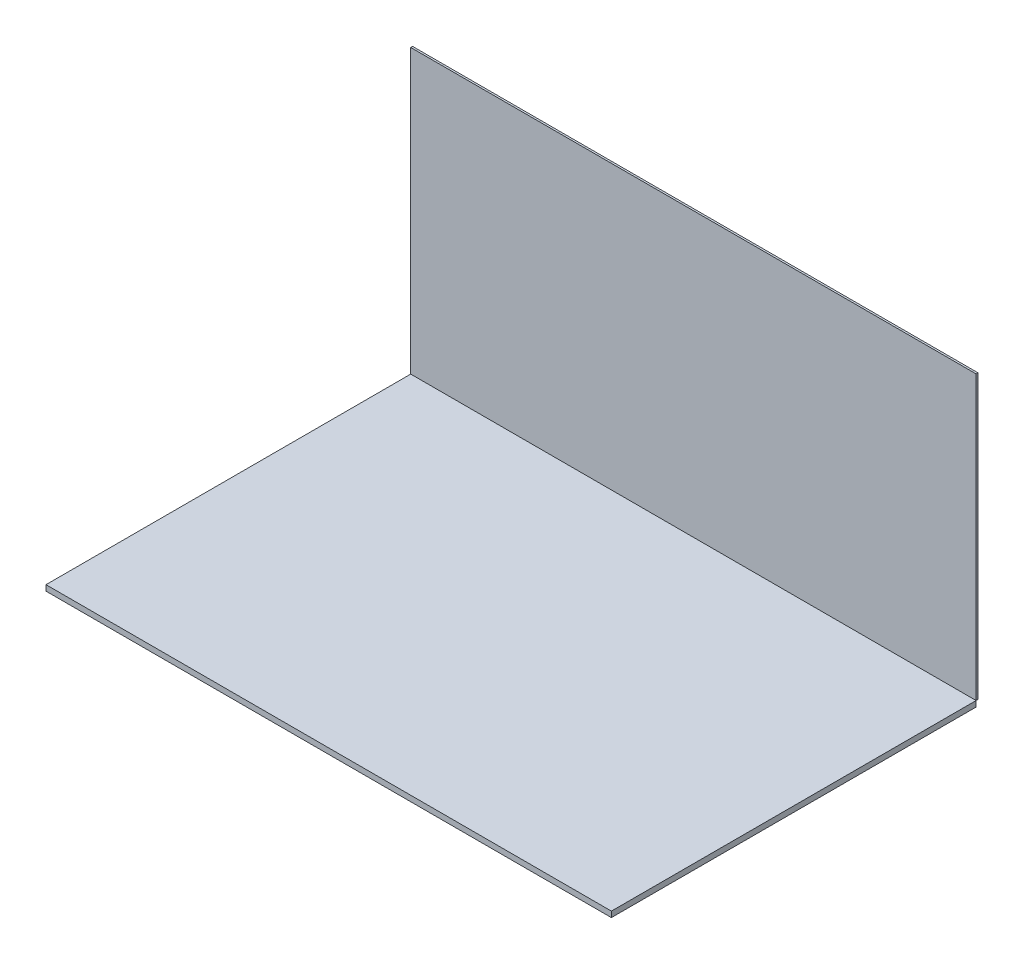
SolidWorks part; units mm, degrees
ref_plane "Front Plane" through (0, 0, 0) normal (0, 0, 1) x (1, 0, 0)
ref_plane "Top Plane" through (0, 0, 0) normal (0, 1, 0) x (1, 0, 0)
ref_plane "Right Plane" through (0, 0, 0) normal (1, 0, 0) x (0, 0, -1)
sketch "Sketch1" plane through (0, 0, 0) normal (0, 1, 0) x (1, 0, 0)
  line L1 (-60.6405, 20.096) -> (15.5127, 20.096)
  line L2 (-60.6405, 20.096) -> (-60.6405, -29.0275)
  line L3 (-60.6405, -29.0275) -> (15.5127, -29.0275)
  line L4 (15.5127, 20.096) -> (15.5127, -29.0275)
extrude "Floor" add sketch "Sketch1" along normal blind 0.762
sketch "Sketch5" plane through (0, 0.762, 0) normal (0, 1, 0) x (1, 0, 0)
  line L0 (15.5127, 20.096) -> (-60.6405, 20.096) construction
  line L1 (15.5127, 20.096) -> (-60.6405, 20.096)
extrude "Wall1" add sketch "Sketch5" along normal blind 38.1 separate body thin
